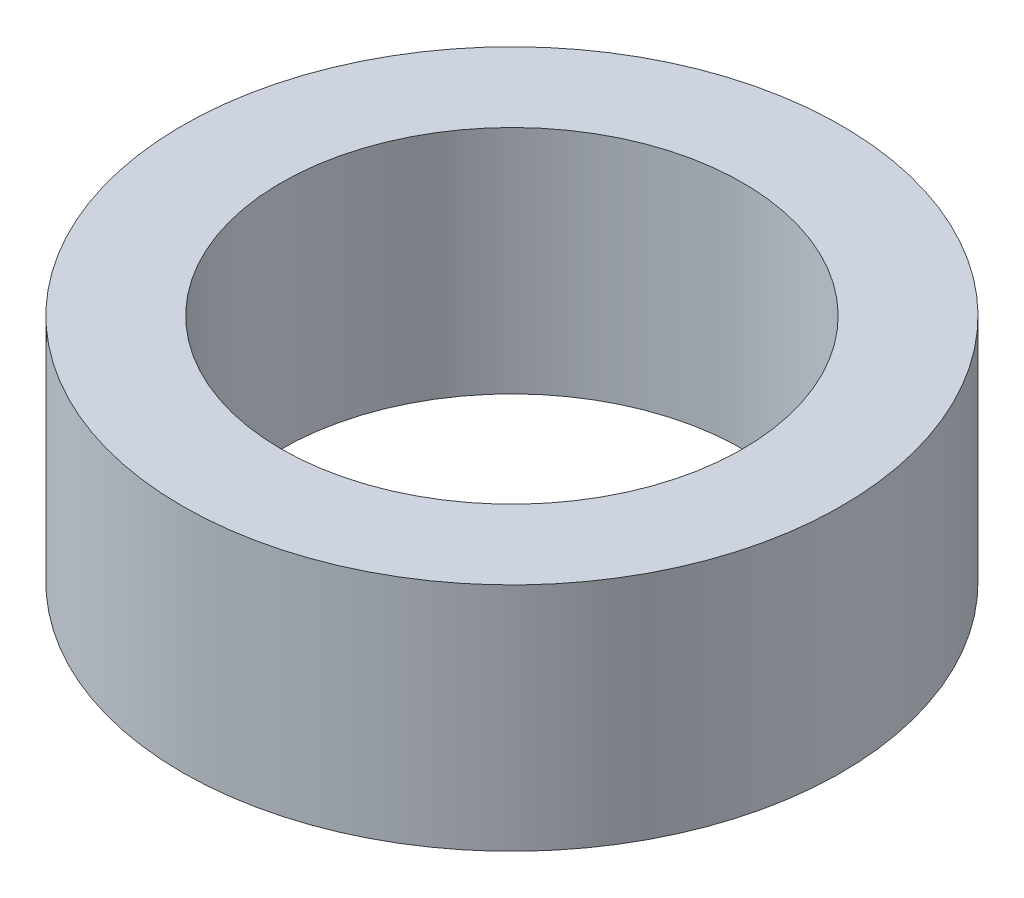
SolidWorks part; units mm, degrees
ref_plane "Front Plane" through (0, 0, 0) normal (0, 0, 1) x (1, 0, 0)
ref_plane "Top Plane" through (0, 0, 0) normal (0, 1, 0) x (1, 0, 0)
ref_plane "Right Plane" through (0, 0, 0) normal (1, 0, 0) x (0, 0, -1)
sketch "Sketch1" plane through (0, 0, 0) normal (0, 1, 0) x (1, 0, 0)
  circle A0 centre (0, 0) radius 12.7
  circle A1 centre (0, 0) radius 8.89
  dimension "D1" = 3.81
extrude "Boss-Extrude1" add sketch "Sketch1" along normal blind 8.89
